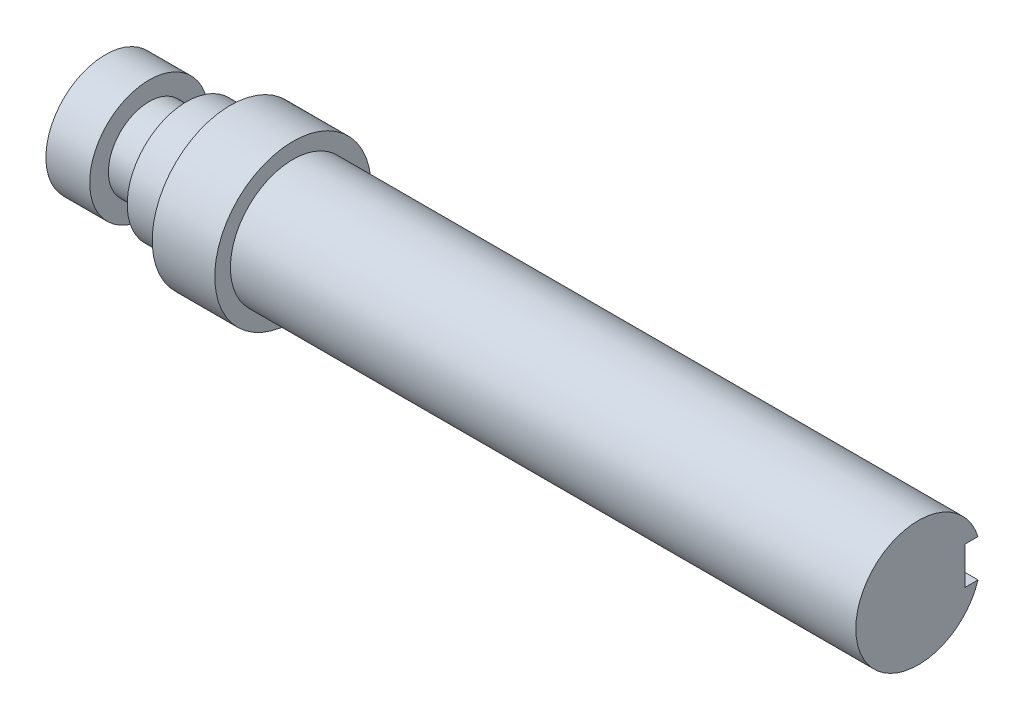
SolidWorks part; units mm, degrees
ref_plane "Ön Düzlem" through (0, 0, 0) normal (0, 0, 1) x (1, 0, 0)
ref_plane "Üst Düzlem" through (0, 0, 0) normal (0, 1, 0) x (1, 0, 0)
ref_plane "Sağ Düzlem" through (0, 0, 0) normal (1, 0, 0) x (0, 0, -1)
sketch "Çizim1" plane through (0, 0, 0) normal (0, 0, 1) x (1, 0, 0)
  line L0 (0, 0) -> (-133.1422, 0) construction
  line L1 (-100, 10) -> (-100, 12.5)
  line L2 (-100, 12.5) -> (-110, 12.5)
  line L3 (-110, 12.5) -> (-110, 9.5)
  line L4 (-110, 9.5) -> (-117, 9.5)
  line L5 (-117, 9.5) -> (-117, 6.5)
  line L6 (-117, 6.5) -> (-123, 6.5)
  line L7 (-123, 6.5) -> (-123, 9.5)
  line L8 (-123, 9.5) -> (-130, 9.5)
  line L9 (-130, 9.5) -> (-130, 0)
  line L10 (-100, 10) -> (0, 10)
  line L11 (0, 10) -> (0, 0)
  line L12 (0, 0) -> (-130, 0)
  dimension "D1" = 10
  dimension "D2" = 100
  dimension "D3" = 12.5
  dimension "D4" = 10
  dimension "D5" = 7
  dimension "D6" = 6
  dimension "D7" = 7
  dimension "D8" = 9.5
  dimension "D9" = 3
revolve "Döndür1" add sketch "Çizim1" angle 360 about L0
ref_plane "Düzlem1" through (0, 0, -10) normal (0, 0, 1) x (1, 0, 0)
sketch "Çizim2" plane through (0, 0, -10) normal (0, 0, 1) x (1, 0, 0)
  line L0 (0, -3) -> (0, 3)
  line L1 (0, -10) -> (0, 10) construction
  line L2 (0, -3) -> (-20, -3)
  line L3 (-20, -3) -> (-20, 3)
  line L4 (-20, 3) -> (0, 3)
  point P6 (0, 0)
  dimension "D1" = 6
  dimension "D2" = 20
extrude "Kes-Ekstrüzyon2" cut sketch "Çizim2" along normal blind 2.5
